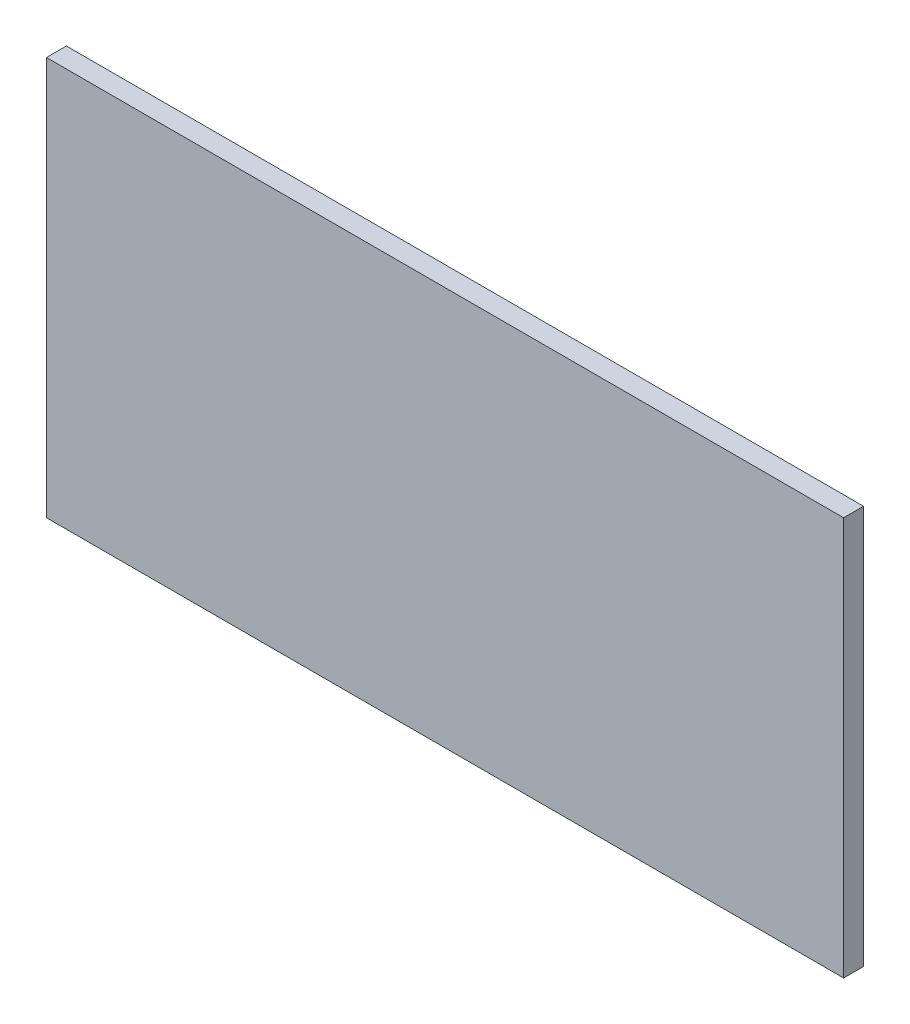
SolidWorks part; units mm, degrees
ref_plane "Alzado" through (0, 0, 0) normal (0, 0, 1) x (1, 0, 0)
ref_plane "Planta" through (0, 0, 0) normal (0, 1, 0) x (1, 0, 0)
ref_plane "Vista lateral" through (0, 0, 0) normal (1, 0, 0) x (0, 0, -1)
sketch "Croquis1" plane through (0, 0, 0) normal (0, 0, 1) x (1, 0, 0)
  line L1 (-60, 30) -> (60, 30)
  line L2 (-60, 30) -> (-60, -30)
  line L3 (-60, -30) -> (60, -30)
  line L4 (60, 30) -> (60, -30)
  line L5 (-60, 30) -> (60, -30) construction
  line L6 (-60, -30) -> (60, 30) construction
  point P0 (0, 0)
  dimension "D1" = 60
  dimension "D2" = 120
extrude "Saliente-Extruir1" add sketch "Croquis1" along normal blind 3
